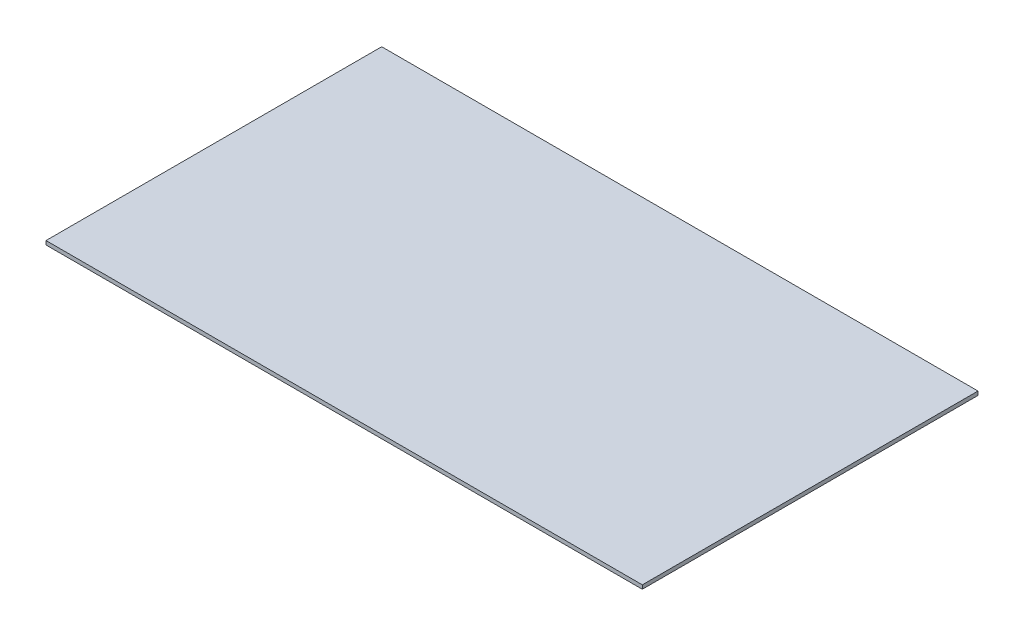
SolidWorks part; units mm, degrees
ref_plane "Front Plane" through (0, 0, 0) normal (0, 0, 1) x (1, 0, 0)
ref_plane "Top Plane" through (0, 0, 0) normal (0, 1, 0) x (1, 0, 0)
ref_plane "Right Plane" through (0, 0, 0) normal (1, 0, 0) x (0, 0, -1)
sketch "Sketch1" plane through (0, 0, 0) normal (0, 1, 0) x (1, 0, 0)
  line L1 (-32.3904, 18.6072) -> (24.8096, 18.6072)
  line L2 (-32.3904, 18.6072) -> (-32.3904, -13.5928)
  line L3 (-32.3904, -13.5928) -> (24.8096, -13.5928)
  line L4 (24.8096, 18.6072) -> (24.8096, -13.5928)
  dimension "D1" = 57.2
  dimension "D2" = 32.2
extrude "Boss-Extrude1" add sketch "Sketch1" along normal blind 0.37
